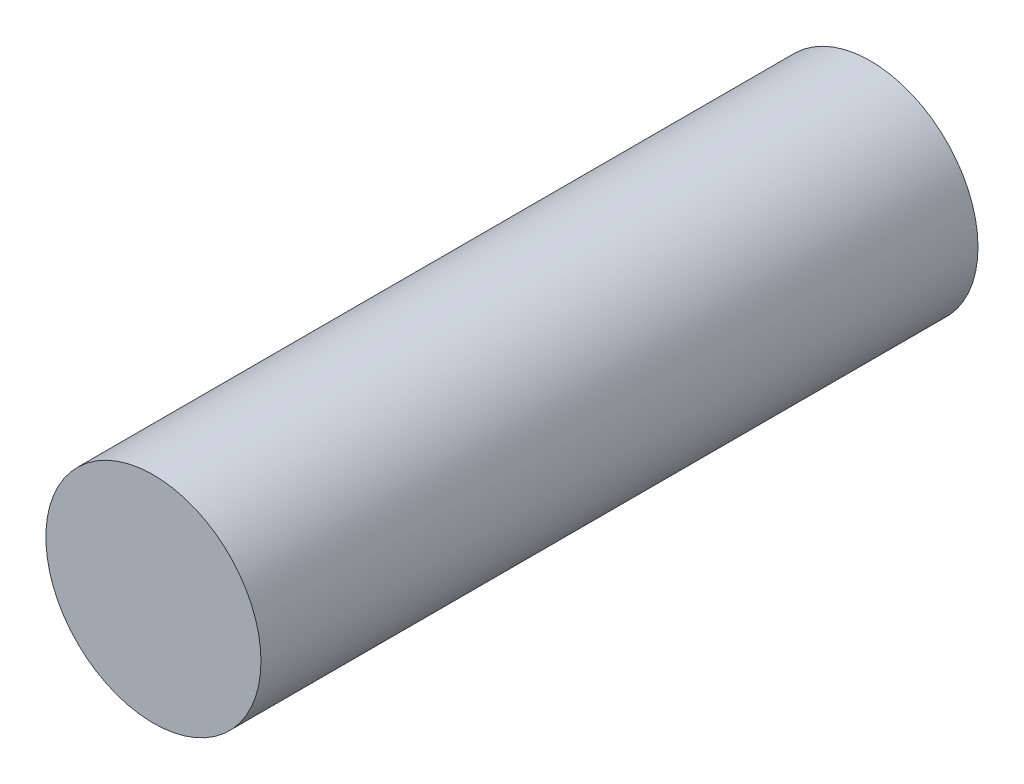
SolidWorks part; units mm, degrees
material "3.0255 (EN-AW 1350A)"
ref_plane "Plan de face" through (0, 0, 0) normal (0, 0, 1) x (1, 0, 0)
ref_plane "Plan de dessus" through (0, 0, 0) normal (0, 1, 0) x (1, 0, 0)
ref_plane "Plan de droite" through (0, 0, 0) normal (1, 0, 0) x (0, 0, -1)
sketch "Esquisse1" plane through (0, 0, 0) normal (0, 0, 1) x (1, 0, 0)
  circle A0 centre (0, 0) radius 3
  dimension "D1" = 6
extrude "Boss.-Extru.1" add sketch "Esquisse1" along normal blind 20
